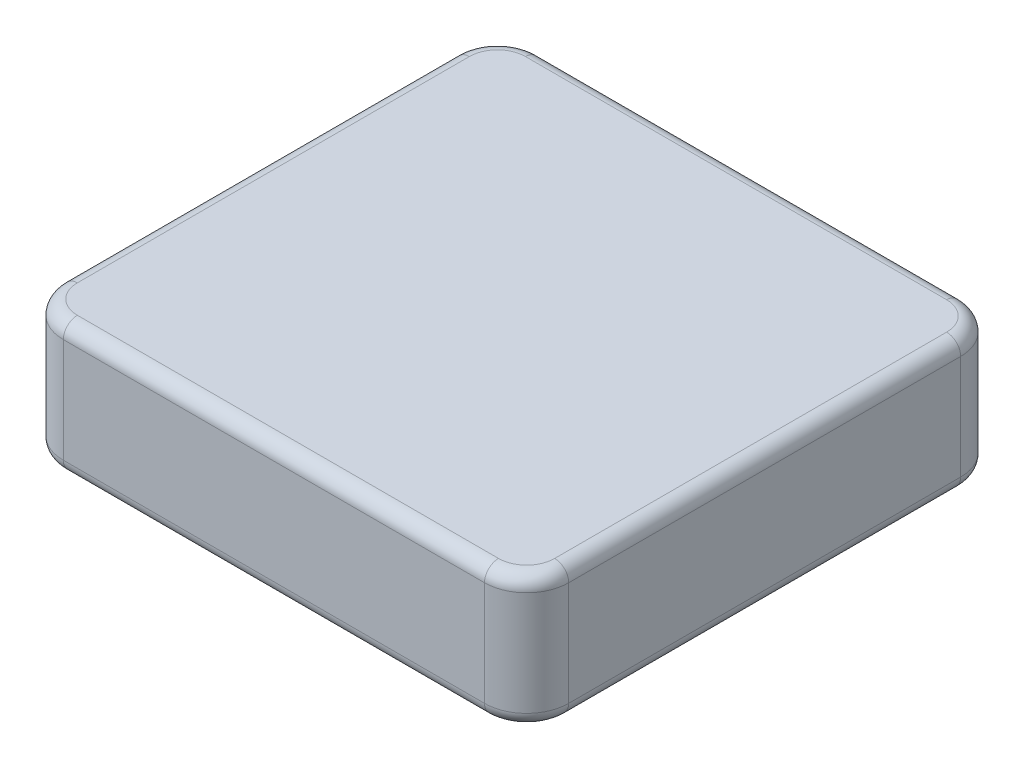
SolidWorks part; units mm, degrees
material "Custom Plastic"
ref_plane "Front Plane" through (0, 0, 0) normal (0, 0, 1) x (1, 0, 0)
ref_plane "Top Plane" through (0, 0, 0) normal (0, 1, 0) x (1, 0, 0)
ref_plane "Right Plane" through (0, 0, 0) normal (1, 0, 0) x (0, 0, -1)
ref_plane "Plane1" through (0, 29.972, 0) normal (0, 1, 0) x (1, 0, 0)
sketch "Sketch1" plane through (0, 29.972, 0) normal (0, 1, 0) x (1, 0, 0)
  line L0 (57.15, -53.848) -> (57.15, 53.848)
  line L1 (57.15, 53.848) -> (-57.15, 53.848)
  line L2 (-57.15, 53.848) -> (-57.15, -53.848)
  line L3 (-57.15, -53.848) -> (57.15, -53.848)
extrude "Boss-Extrude1" add sketch "Sketch1" against normal blind 29.972
fillet "Fillet1" radius 9.525 4 edges at (-57.15, 14.986, -53.848) (57.15, 14.986, -53.848) (-57.15, 14.986, 53.848) (57.15, 14.986, 53.848)
fillet "Fillet2" radius 3.175 16 edges at (54.3602, 0, 51.0582) (57.15, 0, 0) (0, 0, 53.848) (54.3602, 0, -51.0582) (-54.3602, 0, 51.0582) (0, 0, -53.848) (-57.15, 0, 0) (-54.3602, 0, -51.0582) (-54.3602, 29.972, 51.0582) (0, 29.972, 53.848) (-57.15, 29.972, 0) (54.3602, 29.972, 51.0582) (-54.3602, 29.972, -51.0582) (57.15, 29.972, 0) (0, 29.972, -53.848) (54.3602, 29.972, -51.0582)
